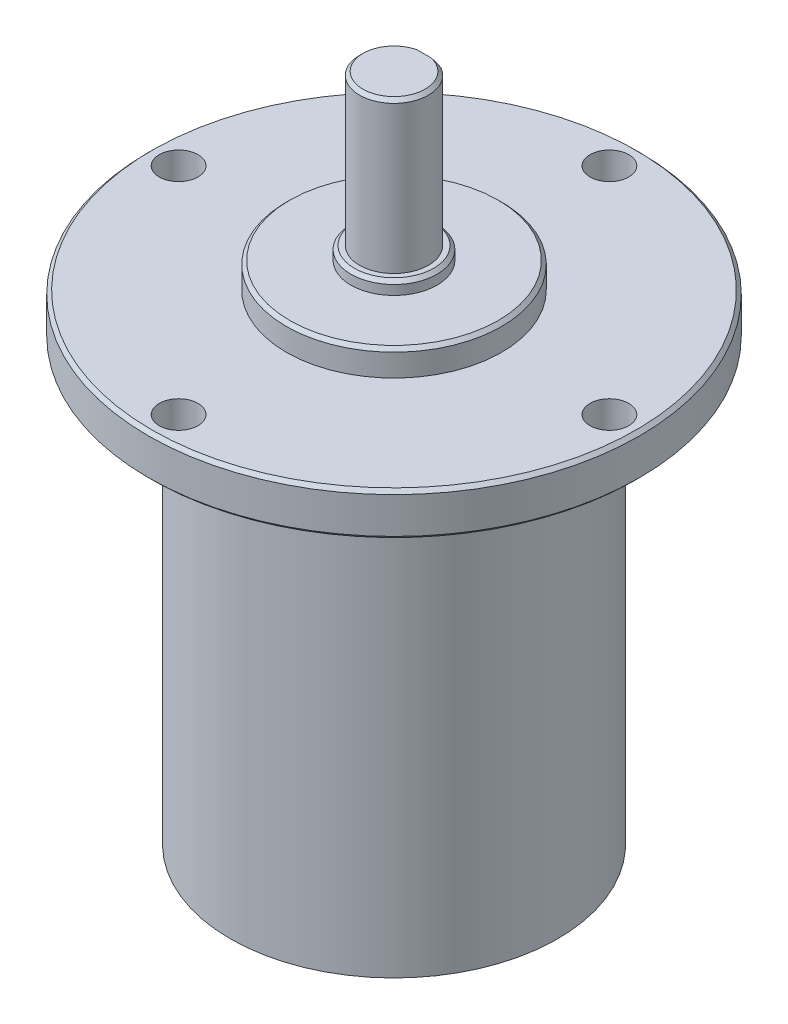
SolidWorks part; units mm, degrees
ref_plane "Front Plane" through (0, 0, 0) normal (0, 0, 1) x (1, 0, 0)
ref_plane "Top Plane" through (0, 0, 0) normal (0, 1, 0) x (1, 0, 0)
ref_plane "Right Plane" through (0, 0, 0) normal (1, 0, 0) x (0, 0, -1)
sketch "Sketch1" plane through (0, 0, 0) normal (0, 0, 1) x (1, 0, 0)
  line L0 (0, 0) -> (0, 92) construction
  line L1 (0, 0) -> (0, -76.0374) construction
  line L2 (0, 0) -> (-19, 0)
  line L3 (-19, 0) -> (-19, 50.7)
  line L4 (-19, 50.7) -> (-28.5, 50.7)
  line L5 (-28.5, 50.7) -> (-28.5, 55.7)
  line L6 (-28.5, 55.7) -> (-12.5, 55.7)
  line L7 (-12.5, 55.7) -> (-12.5, 58.7)
  line L10 (-12.5, 58.7) -> (-5, 58.7)
  line L11 (-5, 58.7) -> (-5, 60.2)
  line L12 (-5, 60.2) -> (0, 60.2)
  line L16 (0, 60.2) -> (0, 0)
  dimension "D1" = 38
  dimension "D2" = 57
  dimension "D3" = 25
  dimension "D4" = 5
  dimension "D5" = 3
  dimension "D6" = 55.7
  dimension "D7" = 1.5
  dimension "D9" = 10
revolve "Revolve1" add sketch "Sketch1" angle 360 about L16
sketch "Sketch2" plane through (0, 60.2, 0) normal (0, 1, 0) x (1, 0, 0)
  line L0 (-1.9365, 3.5) -> (1.9365, 3.5)
  arc A0 (-1.9365, 3.5) -> (1.9365, 3.5) centre (0, 0) ccw
  dimension "D1" = 8
  dimension "D2" = 3.5
extrude "Boss-Extrude1" add sketch "Sketch2" along normal blind 17.5
sketch "Sketch3" plane through (0, 55.7, 0) normal (0, 1, 0) x (1, 0, 0)
  circle A0 centre (0, 0) radius 25 construction
  circle A1 centre (-25, 0) radius 2.25
  circle A2 centre (0, 25) radius 2.25
  circle A3 centre (25, 0) radius 2.25
  circle A4 centre (0, -25) radius 2.25
  dimension "D1" = 50
  dimension "D2" = 4.5
extrude "Cut-Extrude1" cut sketch "Sketch3" against normal through all
chamfer "Chamfer1" distance 0.4 angle 45 3 edges at (0, 50.7, 28.5) (0, 55.7, 28.5) (0, 58.7, 12.5)
chamfer "Chamfer2" distance 0.4 angle 45 1 edges at (0, 77.7, 4)
chamfer "Chamfer3" distance 0.4 angle 45 1 edges at (0, 60.2, 5)
